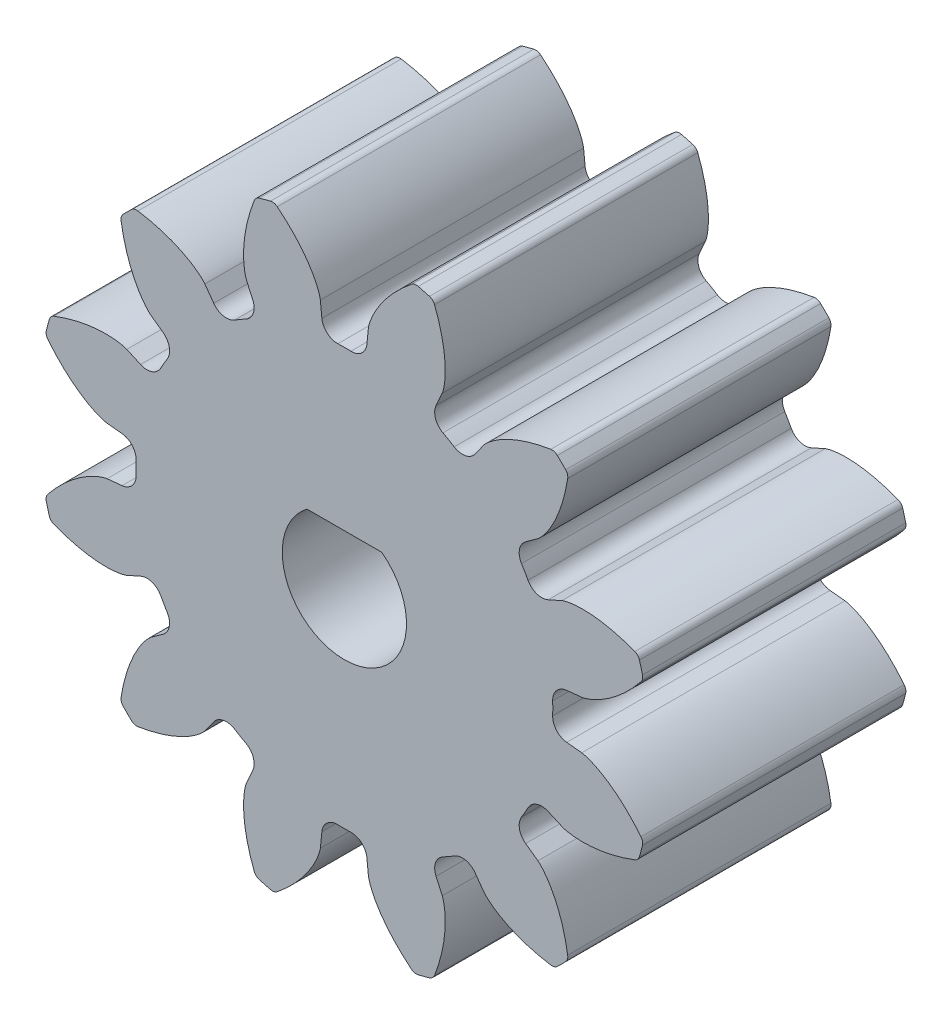
SolidWorks part; units mm, degrees
material "DELRIN"
ref_plane "Front" through (0, 0, 0) normal (0, 0, 1) x (1, 0, 0)
ref_plane "Top" through (0, 0, 0) normal (0, 1, 0) x (1, 0, 0)
ref_plane "Right" through (0, 0, 0) normal (1, 0, 0) x (0, 0, -1)
sketch "Sketch1" plane through (0, 0, 0) normal (0, 0, 1) x (1, 0, 0)
  circle A0 centre (0, 0) radius 14.8167
extrude "Boss-Extrude1" add sketch "Sketch1" along normal blind 12.7
sketch "Sketch3" plane through (0, 0, 0) normal (0, 0, 1) x (1, 0, 0)
  line L0 (0, 0) -> (43.7181, 0) construction
  line L2 (0, 0) -> (-1.013, 10.003) construction
  line L3 (0, 0) -> (1.013, 10.003) construction
  line L4 (1.013, 10.003) -> (1.1597, 11.4515) construction
  line L5 (0, 0) -> (0, 61.276) construction
  line L6 (-1.013, 10.003) -> (-1.1597, 11.4515) construction
  circle A0 centre (0, 0) radius 14.8167 construction
  circle A1 centre (0, 0) radius 12.7 construction
  circle A2 centre (0, 0) radius 11.5101 construction
  arc A3 (1.013, 10.003) -> (-1.013, 10.003) centre (0, 0) ccw construction
  arc A5 (3.383, 14.4253) -> (-3.383, 14.4253) centre (0, 0) ccw
  spline S0 degree 4 poles (-1.1597, 11.4515) (-1.1603, 11.4571) (-1.1625, 11.4726) (-1.1677, 11.5019) (-1.1778, 11.5493) (-1.1932, 11.6092) (-1.2157, 11.6861) (-1.2458, 11.7758) (-1.2825, 11.8733) (-1.3264, 11.9783) (-1.3735, 12.0819) (-1.4237, 12.1841) (-1.4765, 12.2849) (-1.5438, 12.4057) (-1.629, 12.5486) (-1.7352, 12.7127) (-1.8633, 12.8952) (-2.0018, 13.0771) (-2.1447, 13.2526) (-2.2964, 13.4256) (-2.4483, 13.5899) (-2.6134, 13.7559) (-2.7695, 13.9068) (-2.9521, 14.0704) (-3.1018, 14.2009) (-3.3074, 14.367) (-3.4312, 14.4633) (-3.5787, 14.5738) (-3.6457, 14.6217) (-3.6869, 14.6513) knots 0 0 0 0 0 0.005377 0.015084 0.028532 0.04661 0.064855 0.092111 0.119476 0.146842 0.174209 0.201575 0.228941 0.256307 0.307035 0.361767 0.4165 0.471232 0.525964 0.580697 0.635429 0.690161 0.744894 0.799626 0.854358 0.909091 0.954545 1 1 1 1 1 construction
  spline S1 degree 4 poles (-1.1597, 11.4515) (-1.1603, 11.4571) (-1.1625, 11.4726) (-1.1677, 11.5019) (-1.1778, 11.5493) (-1.1932, 11.6092) (-1.2157, 11.6861) (-1.2458, 11.7758) (-1.2825, 11.8733) (-1.3264, 11.9783) (-1.3735, 12.0819) (-1.4237, 12.1841) (-1.4765, 12.2849) (-1.5438, 12.4057) (-1.629, 12.5486) (-1.7352, 12.7127) (-1.8633, 12.8952) (-2.0018, 13.0771) (-2.1447, 13.2526) (-2.2964, 13.4256) (-2.4483, 13.5899) (-2.6134, 13.7559) (-2.7695, 13.9068) (-2.9521, 14.0704) (-3.1018, 14.2009) (-3.2628, 14.331) (-3.3421, 14.3936) (-3.383, 14.4253) knots 0 0 0 0 0 0.005377 0.015084 0.028532 0.04661 0.064855 0.092111 0.119476 0.146842 0.174209 0.201575 0.228941 0.256307 0.307035 0.361767 0.4165 0.471232 0.525964 0.580697 0.635429 0.690161 0.744894 0.799626 0.854358 0.909091 0.909091 0.909091 0.909091 0.909091
  spline S2 degree 4 poles (1.1597, 11.4515) (1.1603, 11.4571) (1.1625, 11.4726) (1.1677, 11.5019) (1.1778, 11.5493) (1.1932, 11.6092) (1.2157, 11.6861) (1.2458, 11.7758) (1.2825, 11.8733) (1.3264, 11.9783) (1.3735, 12.0819) (1.4237, 12.1841) (1.4765, 12.2849) (1.5438, 12.4057) (1.629, 12.5486) (1.7352, 12.7127) (1.8633, 12.8952) (2.0018, 13.0771) (2.1447, 13.2526) (2.2964, 13.4256) (2.4483, 13.5899) (2.6134, 13.7559) (2.7695, 13.9068) (2.9521, 14.0704) (3.1018, 14.2009) (3.3074, 14.367) (3.4312, 14.4633) (3.5787, 14.5738) (3.6457, 14.6217) (3.6869, 14.6513) knots 0 0 0 0 0 0.005377 0.015084 0.028532 0.04661 0.064855 0.092111 0.119476 0.146842 0.174209 0.201575 0.228941 0.256307 0.307035 0.361767 0.4165 0.471232 0.525964 0.580697 0.635429 0.690161 0.744894 0.799626 0.854358 0.909091 0.954545 1 1 1 1 1 construction
  spline S3 degree 4 poles (1.1597, 11.4515) (1.1603, 11.4571) (1.1625, 11.4726) (1.1677, 11.5019) (1.1778, 11.5493) (1.1932, 11.6092) (1.2157, 11.6861) (1.2458, 11.7758) (1.2825, 11.8733) (1.3264, 11.9783) (1.3735, 12.0819) (1.4237, 12.1841) (1.4765, 12.2849) (1.5438, 12.4057) (1.629, 12.5486) (1.7352, 12.7127) (1.8633, 12.8952) (2.0018, 13.0771) (2.1447, 13.2526) (2.2964, 13.4256) (2.4483, 13.5899) (2.6134, 13.7559) (2.7695, 13.9068) (2.9521, 14.0704) (3.1018, 14.2009) (3.2628, 14.331) (3.3421, 14.3936) (3.383, 14.4253) knots 0 0 0 0 0 0.005377 0.015084 0.028532 0.04661 0.064855 0.092111 0.119476 0.146842 0.174209 0.201575 0.228941 0.256307 0.307035 0.361767 0.4165 0.471232 0.525964 0.580697 0.635429 0.690161 0.744894 0.799626 0.854358 0.909091 0.909091 0.909091 0.909091 0.909091
  point P0 (0, 10.0542)
sketch "DCLTBC" plane through (0, 0, 0) normal (0, 0, 1) x (1, 0, 0)
  line L0 (0, 0) -> (41.04, 0) construction
  line L1 (-1.013, 10.003) -> (-1.1597, 11.4515) construction
  line L2 (1.013, 10.003) -> (1.1597, 11.4515) construction
  line L3 (-1.013, 10.003) -> (-1.1597, 11.4515)
  line L4 (1.013, 10.003) -> (1.1597, 11.4515)
  line L5 (0, 0) -> (0, 104.9356) construction
  circle A0 centre (0, 0) radius 14.8167
  circle A1 centre (0, 0) radius 12.7 construction
  circle A2 centre (0, 0) radius 11.5101 construction
  arc A3 (1.013, 10.003) -> (-1.013, 10.003) centre (0, 0) ccw construction
  arc A4 (1.013, 10.003) -> (-1.013, 10.003) centre (0, 0) ccw
  spline S0 degree 4 poles (-994.6421, -102.1305) (-15.3204, 8.3811) (-1.2885, 10.3805) (-1.0584, 10.9911) (-1.1778, 11.5493) (-1.1932, 11.6092) (-1.2157, 11.6861) (-1.2458, 11.7758) (-1.2825, 11.8733) (-1.3264, 11.9783) (-1.3735, 12.0819) (-1.4237, 12.1841) (-1.4765, 12.2849) (-1.5438, 12.4057) (-1.629, 12.5486) (-1.7352, 12.7127) (-1.8633, 12.8952) (-2.0018, 13.0771) (-2.1447, 13.2526) (-2.2964, 13.4256) (-2.4483, 13.5899) (-2.6134, 13.7559) (-2.7695, 13.9068) (-2.9521, 14.0704) (-3.653, 14.6812) (-6.0162, 16.384) (19.2983, -3.4818) (-794.1304, 626.5236) knots -0.502219 -0.502219 -0.502219 -0.502219 -0.502219 0.005377 0.015084 0.028532 0.04661 0.064855 0.092111 0.119476 0.146842 0.174209 0.201575 0.228941 0.256307 0.307035 0.361767 0.4165 0.471232 0.525964 0.580697 0.635429 0.690161 0.744894 0.799626 0.854358 1.715037 1.715037 1.715037 1.715037 1.715037 only from (-1.1597, 11.4515) to (-3.383, 14.4253) construction
  spline S1 degree 4 poles (994.6421, -102.1305) (15.3204, 8.3811) (1.2885, 10.3805) (1.0584, 10.9911) (1.1778, 11.5493) (1.1932, 11.6092) (1.2157, 11.6861) (1.2458, 11.7758) (1.2825, 11.8733) (1.3264, 11.9783) (1.3735, 12.0819) (1.4237, 12.1841) (1.4765, 12.2849) (1.5438, 12.4057) (1.629, 12.5486) (1.7352, 12.7127) (1.8633, 12.8952) (2.0018, 13.0771) (2.1447, 13.2526) (2.2964, 13.4256) (2.4483, 13.5899) (2.6134, 13.7559) (2.7695, 13.9068) (2.9521, 14.0704) (3.653, 14.6812) (6.0162, 16.384) (-19.2983, -3.4818) (794.1304, 626.5236) knots -0.502219 -0.502219 -0.502219 -0.502219 -0.502219 0.005377 0.015084 0.028532 0.04661 0.064855 0.092111 0.119476 0.146842 0.174209 0.201575 0.228941 0.256307 0.307035 0.361767 0.4165 0.471232 0.525964 0.580697 0.635429 0.690161 0.744894 0.799626 0.854358 1.715037 1.715037 1.715037 1.715037 1.715037 only from (1.1597, 11.4515) to (3.383, 14.4253) construction
  spline S2 degree 4 poles (-1.1597, 11.4515) (-1.1603, 11.4571) (-1.1625, 11.4726) (-1.1677, 11.5019) (-1.1778, 11.5493) (-1.1932, 11.6092) (-1.2157, 11.6861) (-1.2458, 11.7758) (-1.2825, 11.8733) (-1.3264, 11.9783) (-1.3735, 12.0819) (-1.4237, 12.1841) (-1.4765, 12.2849) (-1.5438, 12.4057) (-1.629, 12.5486) (-1.7352, 12.7127) (-1.8633, 12.8952) (-2.0018, 13.0771) (-2.1447, 13.2526) (-2.2964, 13.4256) (-2.4483, 13.5899) (-2.6134, 13.7559) (-2.7695, 13.9068) (-2.9521, 14.0704) (-3.1018, 14.2009) (-3.2628, 14.331) (-3.3421, 14.3936) (-3.383, 14.4253) knots 0 0 0 0 0 0.005377 0.015084 0.028532 0.04661 0.064855 0.092111 0.119476 0.146842 0.174209 0.201575 0.228941 0.256307 0.307035 0.361767 0.4165 0.471232 0.525964 0.580697 0.635429 0.690161 0.744894 0.799626 0.854358 0.909091 0.909091 0.909091 0.909091 0.909091
  spline S3 degree 4 poles (1.1597, 11.4515) (1.1603, 11.4571) (1.1625, 11.4726) (1.1677, 11.5019) (1.1778, 11.5493) (1.1932, 11.6092) (1.2157, 11.6861) (1.2458, 11.7758) (1.2825, 11.8733) (1.3264, 11.9783) (1.3735, 12.0819) (1.4237, 12.1841) (1.4765, 12.2849) (1.5438, 12.4057) (1.629, 12.5486) (1.7352, 12.7127) (1.8633, 12.8952) (2.0018, 13.0771) (2.1447, 13.2526) (2.2964, 13.4256) (2.4483, 13.5899) (2.6134, 13.7559) (2.7695, 13.9068) (2.9521, 14.0704) (3.1018, 14.2009) (3.2628, 14.331) (3.3421, 14.3936) (3.383, 14.4253) knots 0 0 0 0 0 0.005377 0.015084 0.028532 0.04661 0.064855 0.092111 0.119476 0.146842 0.174209 0.201575 0.228941 0.256307 0.307035 0.361767 0.4165 0.471232 0.525964 0.580697 0.635429 0.690161 0.744894 0.799626 0.854358 0.909091 0.909091 0.909091 0.909091 0.909091
extrude "Cut-Extrude-DCLTBC" cut sketch "DCLTBC" along normal through all
fillet "Fillet-Tip-DCLTBC" radius 0.3764 2 edges at (3.383, 14.4253, 6.35) (-3.383, 14.4253, 6.35)
fillet "Fillet-Root-DCLTBC" radius 0.7528 2 edges at (-1.013, 10.003, 6.35) (1.013, 10.003, 6.35)
pattern_circular "CirPattern-DCLTBC" count 12 over 360 about axis through (0, 0, 12.7) along (0, 0, 1) of "Cut-Extrude-DCLTBC", "Fillet-Tip-DCLTBC", "Fillet-Root-DCLTBC"
sketch "DCGTBC" [suppressed] plane through (0, 0, 0) normal (0, 0, 1) x (1, 0, 0)
  line L0 (0, 0) -> (41.04, 0) construction
  line L1 (-60.6226, 5.3038) -> (0, 0) construction
  line L2 (0, 0) -> (60.6226, 5.3038) construction
  line L3 (0, 0) -> (-16.5124, 0)
  line L5 (0, 0) -> (0, 104.9356) construction
  circle A0 centre (0, 0) radius 65.6167
  circle A1 centre (0, 0) radius 63.5 construction
  circle A2 centre (0, 0) radius 57.5505 construction
  arc A3 (-0.231, 60.8537) -> (0.231, 60.8537) centre (0, 0) ccw construction
  arc A11 (60.6226, 5.3038) -> (-60.6226, 5.3038) centre (0, 0) ccw
  spline S4 degree 4 poles (999.5281, 37.5164) (15.9379, 54.4029) (0.0707, 55.4419) (-0.2895, 56.6024) (-0.2066, 57.7767) (-0.1929, 57.9173) (-0.1708, 58.0988) (-0.1393, 58.3123) (-0.0988, 58.5468) (-0.0484, 58.8015) (0.0074, 59.0552) (0.0683, 59.3079) (0.1336, 59.5593) (0.2182, 59.8633) (0.3273, 60.227) (0.4659, 60.6511) (0.6363, 61.1305) (0.824, 61.6174) (1.0202, 62.0951) (1.2316, 62.5758) (1.4455, 63.0396) (1.6812, 63.5192) (1.9056, 63.9609) (2.1719, 64.4533) (3.0421, 66.0274) (5.6872, 70.2084) (-15.0429, 35.5301) (520.7458, 920.9699) knots -0.449335 -0.449335 -0.449335 -0.449335 -0.449335 0.005377 0.015084 0.028532 0.04661 0.064855 0.092111 0.119476 0.146842 0.174209 0.201575 0.228941 0.256307 0.307035 0.361767 0.4165 0.471232 0.525964 0.580697 0.635429 0.690161 0.744894 0.799626 0.854358 1.559054 1.559054 1.559054 1.559054 1.559054 only from (-0.2184, 57.5501) to (2.8092, 65.5565) construction
  spline S5 degree 4 poles (-999.5281, 37.5164) (-15.9379, 54.4029) (-0.0707, 55.4419) (0.2895, 56.6024) (0.2066, 57.7767) (0.1929, 57.9173) (0.1708, 58.0988) (0.1393, 58.3123) (0.0988, 58.5468) (0.0484, 58.8015) (-0.0074, 59.0552) (-0.0683, 59.3079) (-0.1336, 59.5593) (-0.2182, 59.8633) (-0.3273, 60.227) (-0.4659, 60.6511) (-0.6363, 61.1305) (-0.824, 61.6174) (-1.0202, 62.0951) (-1.2316, 62.5758) (-1.4455, 63.0396) (-1.6812, 63.5192) (-1.9056, 63.9609) (-2.1719, 64.4533) (-3.0421, 66.0274) (-5.6872, 70.2084) (15.0429, 35.5301) (-520.7458, 920.9699) knots -0.449335 -0.449335 -0.449335 -0.449335 -0.449335 0.005377 0.015084 0.028532 0.04661 0.064855 0.092111 0.119476 0.146842 0.174209 0.201575 0.228941 0.256307 0.307035 0.361767 0.4165 0.471232 0.525964 0.580697 0.635429 0.690161 0.744894 0.799626 0.854358 1.559054 1.559054 1.559054 1.559054 1.559054 only from (0.2184, 57.5501) to (-2.8092, 65.5565) construction
  spline S6 degree 4 poles (-0.2184, 57.5501) (-0.2183, 57.5629) (-0.2176, 57.5987) (-0.2144, 57.6663) (-0.2066, 57.7767) (-0.1929, 57.9173) (-0.1708, 58.0988) (-0.1393, 58.3123) (-0.0988, 58.5468) (-0.0484, 58.8015) (0.0074, 59.0552) (0.0683, 59.3079) (0.1336, 59.5593) (0.2182, 59.8633) (0.3273, 60.227) (0.4659, 60.6511) (0.6363, 61.1305) (0.824, 61.6174) (1.0202, 62.0951) (1.2316, 62.5758) (1.4455, 63.0396) (1.6812, 63.5192) (1.9056, 63.9609) (2.1719, 64.4533) (2.3911, 64.8499) (2.63, 65.2574) (2.7481, 65.4554) (2.8092, 65.5565) knots 0 0 0 0 0 0.005377 0.015084 0.028532 0.04661 0.064855 0.092111 0.119476 0.146842 0.174209 0.201575 0.228941 0.256307 0.307035 0.361767 0.4165 0.471232 0.525964 0.580697 0.635429 0.690161 0.744894 0.799626 0.854358 0.909091 0.909091 0.909091 0.909091 0.909091
  spline S7 degree 4 poles (0.2184, 57.5501) (0.2183, 57.5629) (0.2176, 57.5987) (0.2144, 57.6663) (0.2066, 57.7767) (0.1929, 57.9173) (0.1708, 58.0988) (0.1393, 58.3123) (0.0988, 58.5468) (0.0484, 58.8015) (-0.0074, 59.0552) (-0.0683, 59.3079) (-0.1336, 59.5593) (-0.2182, 59.8633) (-0.3273, 60.227) (-0.4659, 60.6511) (-0.6363, 61.1305) (-0.824, 61.6174) (-1.0202, 62.0951) (-1.2316, 62.5758) (-1.4455, 63.0396) (-1.6812, 63.5192) (-1.9056, 63.9609) (-2.1719, 64.4533) (-2.3911, 64.8499) (-2.63, 65.2574) (-2.7481, 65.4554) (-2.8092, 65.5565) knots 0 0 0 0 0 0.005377 0.015084 0.028532 0.04661 0.064855 0.092111 0.119476 0.146842 0.174209 0.201575 0.228941 0.256307 0.307035 0.361767 0.4165 0.471232 0.525964 0.580697 0.635429 0.690161 0.744894 0.799626 0.854358 0.909091 0.909091 0.909091 0.909091 0.909091
  dimension "D1" = 5
  dimension "D2" = 5
extrude "Cut-Extrude-DCGTBC" [suppressed] cut sketch "DCGTBC" along normal through all
fillet "Fillet-Tip-DCGTBC" [suppressed] radius 0.3764
pattern_circular "CirPattern-DCGTBC" [suppressed] count 12 over 360
sketch "Sketch8" plane through (0, 0, 0) normal (0, 0, 1) x (1, 0, 0)
  line L0 (18.125, -4.6) -> (21.725, -4.6)
  line L1 (-1.8034, 2.3939) -> (1.8034, 2.3939)
  circle A2 centre (19.925, -7) radius 3
  circle A3 centre (0, 0) radius 2.9972
  dimension "D1" = 6
  dimension "D2" = 5.9944
  dimension "D3" = 3.6
  dimension "D4" = 3.6068
extrude "Cut-Extrude5" cut sketch "Sketch8" along normal blind 25.4
equation "\"DiametralPitch\"= 12'Diametral Pitch"
equation "\"NumTeeth\"= 12'Number of Teeth"
equation "\"PressureAngle\"= 25deg'Pressure Angle"
equation "\"Addendum\"= 1 / \"DiametralPitch\"'Addendum"
equation "\"Dedendum\"= 1.25 / \"DiametralPitch\"'Dedendum"
equation "\"WorkingDepth\"= 2 / \"DiametralPitch\"'Working Depth - here for REF (Not used in building model)"
equation "\"WholeDepth\"= 2.25 / \"DiametralPitch\"'Whole Depth - here for REF (Not used in building model)"
equation "\"Clearance\"= .25 / \"DiametralPitch\"'Clearance"
equation "\"CircularPitch\"= pi / \"DiametralPitch\"'Circular Pitch - here for REF (Not used in building model)"
equation "\"PitchCircle\"= \"NumTeeth\" / \"DiametralPitch\"'Pitch Circle - or - Pitch Diameter"
equation "\"OutsideDiameter\"= ( \"NumTeeth\" + 2 ) / \"DiametralPitch\"'Outside Diameter"
equation "\"Fillet_Root\"= \"Clearance\" * cos ( \"PressureAngle\" ) * tan ( ( 90 + \"PressureAngle\" ) / 2 ) 'Fillet Root"
equation "\"AddendumCircle\"= \"PitchCircle\" + ( 2 * \"Addendum\" )'Addendum Circle - or - Addendum Diameter"
equation "\"DedendumCircle\"= \"PitchCircle\" - ( 2 * \"Dedendum\" )'Dedendum Circle - or - Dedendum Diameter"
equation "\"BaseCircle\"= \"PitchCircle\" * cos ( \"PressureAngle\" )'Base Circle - Base Diameter"
equation "\"PitchAngle\"= 360deg / \"NumTeeth\"'Pitch Angle"
equation "\"Alpha\"= sqr ( \"PitchCircle\" ^ 2 - \"BaseCircle\" ^ 2 ) / \"BaseCircle\" * 180 / PI - \"PressureAngle\"'Alpha - Used for Calculating Beta"
equation "\"Beta\"= ( \"PitchAngle\" / 4 - ( \"Alpha\" - 90 ) )'Beta - Used in definition of the parameters for the parametric equation driven curve"
equation "\"Gamma\"= ( \"PitchAngle\" / 4 - ( \"Alpha\" + 90 ) )'Gamma - Used in definition of the parameters for the parametric equation driven curve"
equation "\"Phi\"= sqr ( ( \"AddendumCircle\" / 2 ) ^ 2 - ( \"BaseCircle\" / 2 ) ^ 2 ) / ( \"BaseCircle\" / 2 )'Phi - Used in definition of the parameters for the parametric equation driven curve"
equation "\"DCGTBC\"= iif ( \"DedendumCircle\" > \"BaseCircle\" , \"unsuppressed\" , \"suppressed\" )'if Dedendum Circle IS GREATER THAN BaseCircle THEN UnsuppressORSuppress FEATURE"
equation "\"DCLTBC\"= iif ( \"DedendumCircle\" - .002 > \"BaseCircle\" , \"suppressed\" , \"unsuppressed\" )'if Dedendum Circle - .002 IS GREATER THAN BaseCircle THEN SuppressORUnsuppress FEATURE"
equation "\"Cut-Extrude-DCGTBC\"= iif ( \"DedendumCircle\" > \"BaseCircle\" , \"unsuppressed\" , \"suppressed\" )'if Dedendum Circle IS GREATER THAN BaseCircle THEN UnsuppressORSuppress FEATURE"
equation "\"Cut-Extrude-DCLTBC\"= iif ( \"DedendumCircle\" - .002 > \"BaseCircle\" , \"suppressed\" , \"unsuppressed\" )'if Dedendum Circle - .002 IS GREATER THAN BaseCircle THEN SuppressORUnsuppress FEATURE"
equation "\"CirPattern-DCGTBC\"= iif ( \"DedendumCircle\" > \"BaseCircle\" , \"unsuppressed\" , \"suppressed\" )'if Dedendum Circle IS GREATER THAN BaseCircle THEN UnsuppressORSuppress FEATURE"
equation "\"CirPattern-DCLTBC\"= iif ( \"DedendumCircle\" - .002 > \"BaseCircle\" , \"suppressed\" , \"unsuppressed\" )'if Dedendum Circle - .002 IS GREATER THAN BaseCircle THEN SuppressORUnsuppress FEATURE"
equation "\"Fillet-Tip-DCGTBC\"= iif ( \"DedendumCircle\" > \"BaseCircle\" , \"unsuppressed\" , \"suppressed\" )'if Dedendum Circle IS GREATER THAN BaseCircle THEN UnsuppressORSuppress FEATURE"
equation "\"Fillet-Tip-DCLTBC\"= iif ( \"DedendumCircle\" - .002 > \"BaseCircle\" , \"suppressed\" , \"unsuppressed\" )'if Dedendum Circle - .002 IS GREATER THAN BaseCircle THEN SuppressORUnsuppress FEATURE"
equation "\"Fillet-Root-DCLTBC\"= iif ( \"DedendumCircle\" - .002 > \"BaseCircle\" , \"suppressed\" , \"unsuppressed\" )'if Dedendum Circle - .002 IS GREATER THAN BaseCircle THEN SuppressORUnsuppress FEATURE"
equation "\"D1@CirPattern-DCGTBC\"= \"NumTeeth\"'Number of Teeth"
equation "\"D1@CirPattern-DCLTBC\"= \"NumTeeth\"'Number of Teeth"
equation "\"D1@Fillet-Tip-DCGTBC\"= \"Fillet_Root\" / 2 'Tip Rad For Large No of Teeth"
equation "\"D1@Fillet-Tip-DCLTBC\"=\"Fillet_Root\" / 2'Tip Rad For Small No of Teeth"
equation "\"D1@Fillet-Root-DCLTBC\"= \"Fillet_Root\"'Fillet Root"
